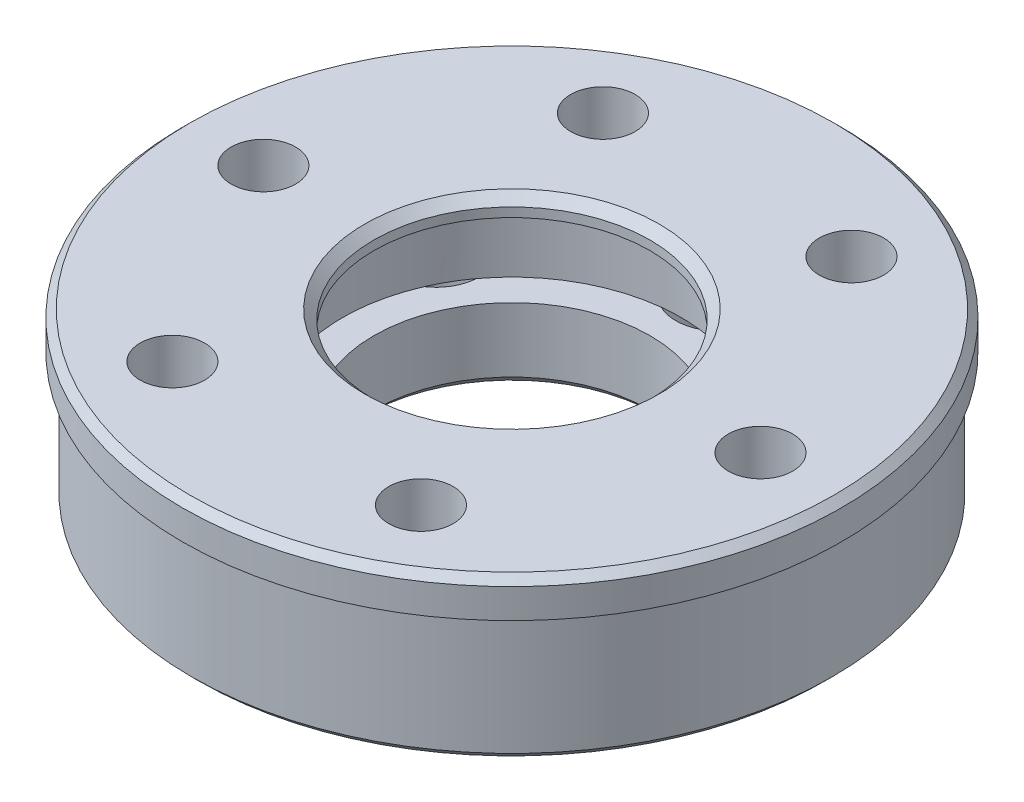
SolidWorks part; units mm, degrees
ref_plane "Front Plane" through (0, 0, 0) normal (0, 0, 1) x (1, 0, 0)
ref_plane "Top Plane" through (0, 0, 0) normal (0, 1, 0) x (1, 0, 0)
ref_plane "Right Plane" through (0, 0, 0) normal (1, 0, 0) x (0, 0, -1)
sketch "Sketch1" plane through (0, 0, 0) normal (0, 1, 0) x (1, 0, 0)
  circle A0 centre (0, 0) radius 13.5 construction
  circle A1 centre (13.5, 0) radius 1.75
  circle A2 centre (6.75, -11.6913) radius 1.75
  circle A3 centre (-6.75, -11.6913) radius 1.75
  circle A4 centre (-13.5, 0) radius 1.75
  circle A5 centre (-6.75, 11.6913) radius 1.75
  circle A6 centre (6.75, 11.6913) radius 1.75
  circle A7 centre (0, 0) radius 17.4
  circle A8 centre (0, 0) radius 7.5
  point P17 (0, 0)
  dimension "D1" = 27
  dimension "D2" = 3.5
  dimension "D4" = 34.8
  dimension "D5" = 15
  dimension "D3" = 6
extrude "Boss-Extrude1" add sketch "Sketch1" along normal mid plane 9
sketch "Sketch2" plane through (0, 0, 0) normal (0, 1, 0) x (1, 0, 0)
  circle A0 centre (0, 0) radius 9.2
  dimension "D1" = 18.4
extrude "Cut-Extrude1" cut sketch "Sketch2" along normal blind 4 from offset 0.5 offset against normal yes
sketch "Sketch3" plane through (0, -4.5, 0) normal (0, -1, 0) x (1, 0, 0)
  circle A0 centre (0, 0) radius 11.75
  circle A1 centre (0, 0) radius 15.25
  circle A2 centre (-13.5, 0) radius 1.75 construction
extrude "Boss-Extrude2" add sketch "Sketch3" against normal blind 1.5
chamfer "Chamfer1" distance 0.5 angle 45 2 edges at (0, -4.5, 7.5) (0, 4.5, 7.5)
sketch "Sketch4" plane through (0, 4.5, 0) normal (0, 1, 0) x (1, 0, 0)
  circle A0 centre (0, 0) radius 17.9
  circle A1 centre (0, 0) radius 17.4 construction
  circle A2 centre (0, 0) radius 17.4
  dimension "D1" = 0.5
extrude "Boss-Extrude3" add sketch "Sketch4" against normal blind 2
sketch "Sketch5" plane through (0, -4.5, 0) normal (0, -1, 0) x (-1, 0, 0)
  line L0 (0, 0) -> (-9.7428, -5.625) construction
  line L1 (0, 0) -> (-11.25, 0) construction
  circle A0 centre (0, 0) radius 11.25 construction
  circle A1 centre (-9.7428, -5.625) radius 2.35
  circle A2 centre (-9.7428, 5.625) radius 2.35
  circle A3 centre (0, 11.25) radius 2.35
  circle A4 centre (9.7428, 5.625) radius 2.35
  circle A5 centre (9.7428, -5.625) radius 2.35
  circle A6 centre (0, -11.25) radius 2.35
  point P18 (0, 0)
  dimension "D1" = 4.7
  dimension "D2" = 22.5
  dimension "D3" = 30
  dimension "D4" = 6
extrude "Cut-Extrude2" cut sketch "Sketch5" against normal blind 4
chamfer "Chamfer2" [suppressed] distance 4 angle 45
chamfer "Chamfer3" distance 0.4 angle 45 2 edges at (0, 4.5, 17.9) (0, -4.5, 17.4)
equation "\"D5@Sketch1\"=18-3"
